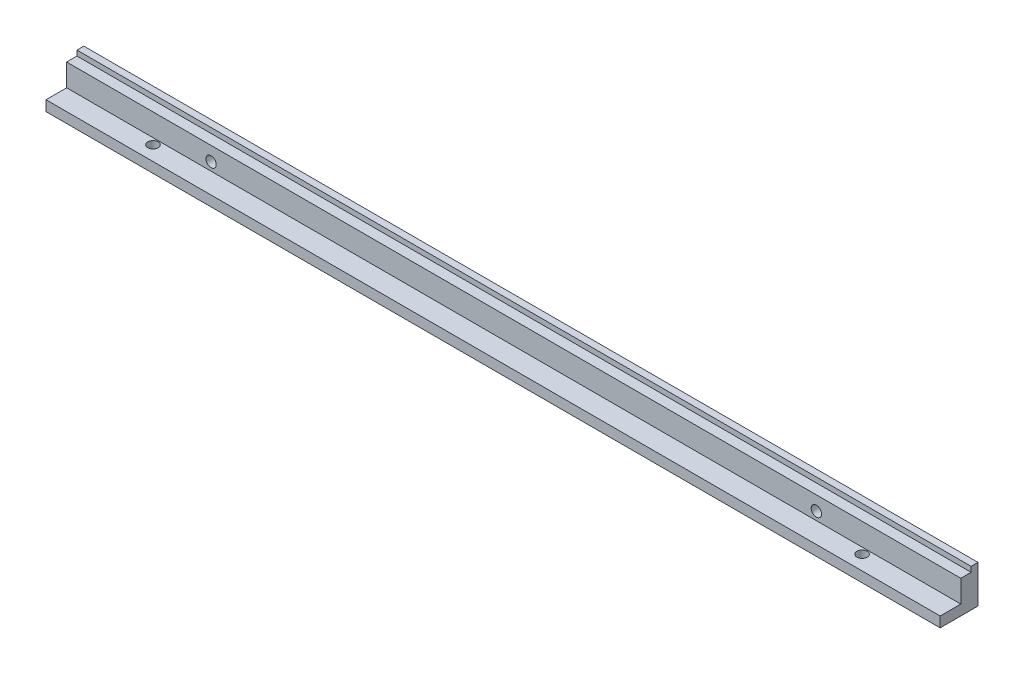
SolidWorks part; units mm, degrees
ref_plane "Спереди" through (0, 0, 0) normal (0, 0, 1) x (1, 0, 0)
ref_plane "Сверху" through (0, 0, 0) normal (0, 1, 0) x (1, 0, 0)
ref_plane "Справа" through (0, 0, 0) normal (1, 0, 0) x (0, 0, -1)
sketch "Эскиз1" plane through (0, 0, 0) normal (1, 0, 0) x (0, 0, -1)
  line L0 (0, 0) -> (-11, 0)
  line L1 (-11, 0) -> (-11, 3)
  line L2 (-11, 3) -> (-5, 3)
  line L3 (-5, 3) -> (-5, 9.5)
  line L4 (-5, 9.5) -> (-2, 9.5)
  line L5 (-2, 9.5) -> (-2, 11)
  line L6 (-2, 11) -> (0, 11)
  line L7 (0, 11) -> (0, 0)
  dimension "D1" = 5
  dimension "D2" = 11
  dimension "D3" = 3
  dimension "D4" = 6
  dimension "D5" = 6.5
  dimension "D6" = 11
  dimension "D7" = 1.5
  dimension "D8" = 2
extrude "Бобышка-Вытянуть1" add sketch "Эскиз1" along normal blind 260
sketch "Эскиз4" plane through (0, 0, 5) normal (0, 0, 1) x (1, 0, 0)
  line L0 (0, 9.5) -> (0, 3) construction
  line L2 (260, 0) -> (0, 0) construction
  line L3 (130, 11) -> (130, -1.6462) construction
  line L4 (260, 11) -> (0, 11) construction
  circle A0 centre (42, 5.4) radius 1.5
  circle A1 centre (218, 5.4) radius 1.5
  dimension "D1" = 3
  dimension "D2" = 42
  dimension "D3" = 5.4
extrude "Вырез-Вытянуть3" cut sketch "Эскиз4" against normal through all
sketch "Эскиз5" plane through (0, 3, 0) normal (0, 1, 0) x (1, 0, 0)
  line L0 (0, -5) -> (0, -11) construction
  line L3 (260, -11) -> (0, -11) construction
  line L4 (130, -11) -> (130, 0) construction
  circle A0 centre (26.91, -6.8) radius 1.5
  circle A1 centre (233.09, -6.8) radius 1.5
  dimension "D1" = 3
  dimension "D2" = 26.91
  dimension "D3" = 4.2
extrude "Вырез-Вытянуть4" cut sketch "Эскиз5" against normal through all
